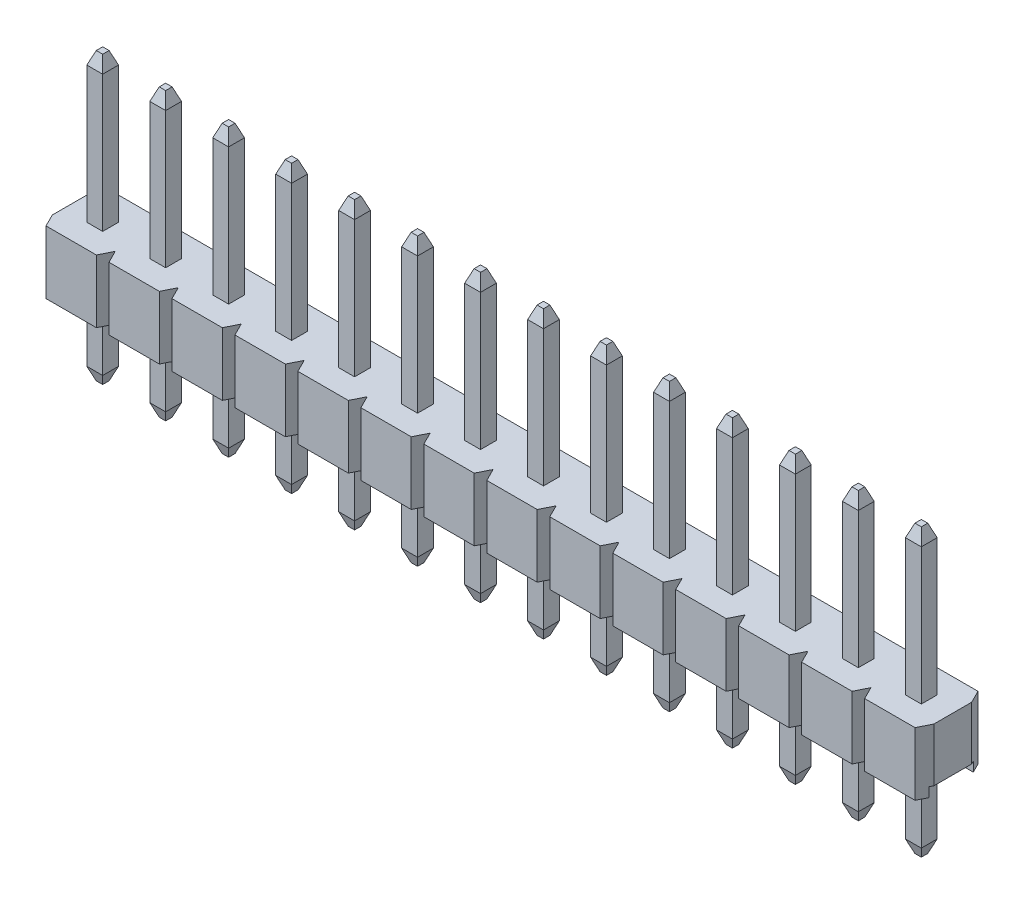
SolidWorks part; units mm, degrees
ref_plane "Front Plane" through (0, 0, 0) normal (0, 0, 1) x (1, 0, 0)
ref_plane "Top Plane" through (0, 0, 0) normal (0, 1, 0) x (1, 0, 0)
ref_plane "Right Plane" through (0, 0, 0) normal (1, 0, 0) x (0, 0, -1)
sketch "Sketch1" plane through (0, 0, 0) normal (0, 1, 0) x (1, 0, 0)
  line L1 (0, 0) -> (2.54, 0)
  line L2 (0, 0) -> (0, 2.54)
  line L3 (0, 2.54) -> (2.54, 2.54)
  line L4 (2.54, 0) -> (2.54, 2.54)
  dimension "D1" = 2.54
  dimension "D2" = 2.54
extrude "Main Body" add sketch "Sketch1" along normal blind 2.54
sketch "Sketch3" plane through (0, 0, 0) normal (-1, 0, 0) x (0, 0, 1)
  line L0 (-2.54, 0) -> (0, 0) construction
  line L1 (-2.159, 0) -> (-0.381, 0)
  line L2 (-2.159, 0) -> (-2.159, 0.381)
  line L3 (-2.159, 0.381) -> (-0.381, 0.381)
  line L4 (-0.381, 0) -> (-0.381, 0.381)
  line L5 (-2.54, 0) -> (-2.159, 0) construction
  line L6 (-0.381, 0) -> (0, 0) construction
  dimension "D1" = 0.381
extrude "Cut-Extrude1" cut sketch "Sketch3" against normal through all
sketch "Sketch4" plane through (0, 2.54, 0) normal (0, 1, 0) x (1, 0, 0)
  line L0 (0, 2.54) -> (0, 2.032)
  line L1 (0, 2.54) -> (0, 0) construction
  line L2 (0, 2.032) -> (0.254, 2.54)
  line L3 (2.54, 2.54) -> (0, 2.54) construction
  line L4 (0.254, 2.54) -> (0, 2.54)
  line L5 (2.54, 2.54) -> (2.286, 2.54)
  line L6 (2.286, 2.54) -> (2.54, 2.032)
  line L7 (2.54, 0) -> (2.54, 2.54) construction
  line L8 (2.54, 2.032) -> (2.54, 2.54)
  line L9 (2.54, 0) -> (2.286, 0)
  line L10 (0, 0) -> (2.54, 0) construction
  line L11 (2.286, 0) -> (2.54, 0.508)
  line L12 (2.54, 0.508) -> (2.54, 0)
  line L14 (0, 0) -> (0, 0.508)
  line L15 (0, 0.508) -> (0.254, 0)
  line L16 (0.254, 0) -> (0, 0)
  line M1 (0, 2.54) -> (0, 0)
  line M2 (0, 0) -> (2.54, 0)
  line M3 (2.54, 0) -> (2.54, 2.54)
  line M4 (2.54, 2.54) -> (0, 2.54)
  dimension "D1" = 0.254
  dimension "D2" = 0.508
extrude "Cut-Extrude2" cut sketch "Sketch4" against normal through all contours L2 M1 M4 | L6 M4 M3 | L15 M1 M2 | L9 L11 L12
pattern_linear "Body Pattern" count 14 spacing 2.54 along (-1, 0, 0) of "Main Body", "Cut-Extrude1", "Cut-Extrude2"
sketch "Sketch2" plane through (0, 2.54, 0) normal (0, 1, 0) x (1, 0, 0)
  line L0 (1.27, 2.54) -> (1.27, 1.59) construction
  line L1 (0.95, 0.95) -> (1.59, 0.95)
  line L2 (0.95, 0.95) -> (0.95, 1.59)
  line L3 (0.95, 1.59) -> (1.59, 1.59)
  line L4 (1.59, 0.95) -> (1.59, 1.59)
  line L6 (2.286, 2.54) -> (0.254, 2.54) construction
  line L8 (1.27, 0.95) -> (1.27, 0) construction
  line L9 (0.254, 0) -> (2.286, 0) construction
  dimension "D1" = 0.64
extrude "Pin" add sketch "Sketch2" along normal blind 6 and the other way offset from surface (5.54 mm away) 3 other way up to face at (1.27, 0, -0.1905)
chamfer "Chamfer1" distance 0.508 distance2 0.1905 4 edges at (0.95, 8.54, -1.27) (1.27, 8.54, -1.59) (1.59, 8.54, -1.27) (1.27, 8.54, -0.95)
chamfer "Chamfer2" distance 0.1905 distance2 0.508 4 edges at (1.27, -3, -1.59) (1.59, -3, -1.27) (1.27, -3, -0.95) (0.95, -3, -1.27)
pattern_linear "Pin Pattern" count 14 spacing 2.54 along (-1, 0, 0) of "Pin", "Chamfer1", "Chamfer2"
